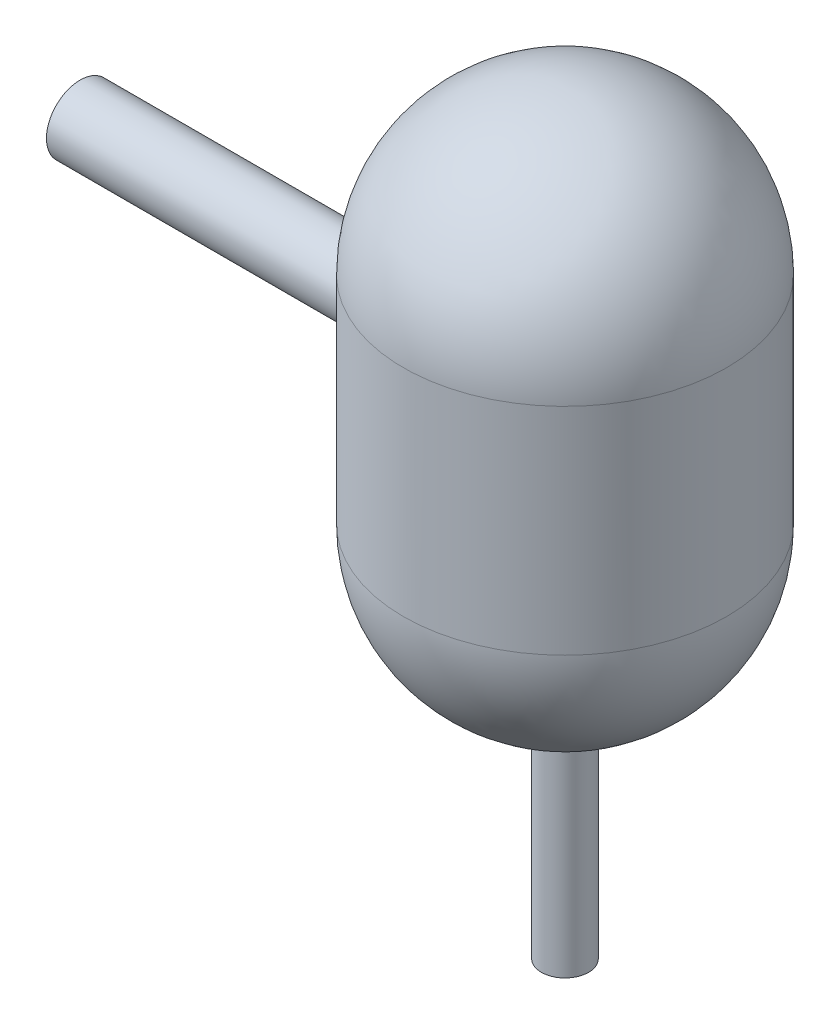
SolidWorks part; units mm, degrees
material "Plain Carbon Steel"
ref_plane "Front Plane" through (0, 0, 0) normal (0, 0, 1) x (1, 0, 0)
ref_plane "Top Plane" through (0, 0, 0) normal (0, 1, 0) x (1, 0, 0)
ref_plane "Right Plane" through (0, 0, 0) normal (1, 0, 0) x (0, 0, -1)
sketch "Sketch1" plane through (0, 0, 0) normal (0, 0, 1) x (1, 0, 0)
  line L0 (-152.4, 101.6) -> (-152.4, -101.6)
  line L1 (0, -254) -> (0, -247.65)
  line L2 (-146.05, 101.6) -> (-146.05, -101.6)
  line L3 (0, 247.65) -> (0, 254)
  arc A0 (0, 254) -> (-152.4, 101.6) centre (0, 101.6) ccw
  arc A1 (0, -254) -> (-152.4, -101.6) centre (0, -101.6) cw
  arc A2 (0, 247.65) -> (-146.05, 101.6) centre (0, 101.6) ccw
  arc A3 (0, -247.65) -> (-146.05, -101.6) centre (0, -101.6) cw
  dimension "D1" = 152.4
  dimension "D5" = 101.6
  dimension "D2" = 6.35
  dimension "D3" = 203.2
  dimension "D4" = 508
  dimension "D6" = 6.35
  dimension "D7" = 6.35
revolve "Revolve1" add sketch "Sketch1" angle 360 about L1
sketch "Sketch2" plane through (0, 0, 0) normal (1, 0, 0) x (0, 0, -1)
  circle A0 centre (0, 0) radius 25.4
  dimension "D1" = 50.8
extrude "Cut-Extrude1" cut sketch "Sketch2" against normal up to next
ref_plane "Plane1" through (-457.2, 0, 0) normal (1, 0, 0) x (0, 0, -1)
sketch "Sketch4" plane through (-457.2, 0, 0) normal (1, 0, 0) x (0, 0, -1)
  circle A0 centre (0, 0) radius 25.4 construction
  circle A1 centre (0, 0) radius 25.4
  circle A2 centre (0, 0) radius 31.75
  dimension "D1" = 6.35
extrude "Boss-Extrude3" add sketch "Sketch4" along normal up to surface (306.9316 mm away)
ref_plane "Plane2" through (0, -457.2, 0) normal (0, 1, 0) x (1, 0, 0)
sketch "Sketch5" plane through (0, -457.2, 0) normal (0, 1, 0) x (1, 0, 0)
  circle A0 centre (0, 0) radius 15.875
  dimension "D1" = 31.75
extrude "Cut-Extrude2" cut sketch "Sketch5" along normal up to surface (210.4153 mm away)
sketch "Sketch6" plane through (0, -457.2, 0) normal (0, 1, 0) x (1, 0, 0)
  circle A0 centre (0, 0) radius 15.875 construction
  circle A1 centre (0, 0) radius 15.875
  circle A2 centre (0, 0) radius 22.225
  dimension "D1" = 6.35
extrude "Boss-Extrude4" add sketch "Sketch6" along normal up to surface (210.4153 mm away)
